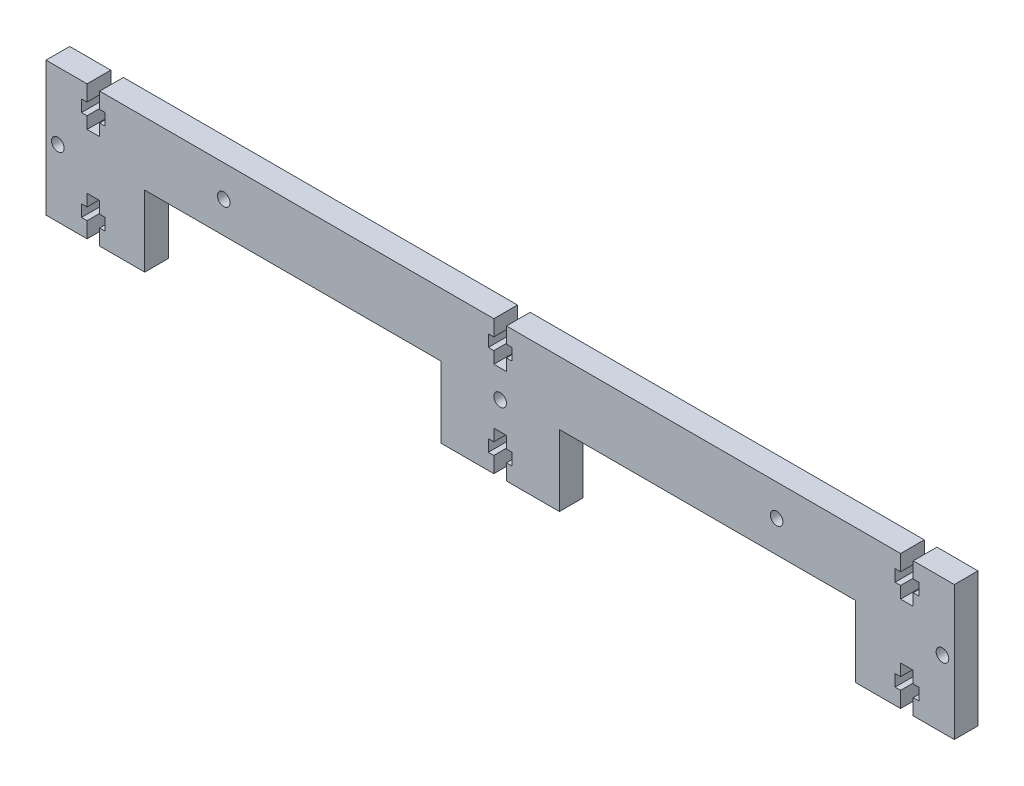
SolidWorks part; units mm, degrees
material "Balsa"
ref_plane "Plano frontal" through (0, 0, 0) normal (0, 0, 1) x (1, 0, 0)
ref_plane "Plano superior" through (0, 0, 0) normal (0, 1, 0) x (1, 0, 0)
ref_plane "Plano direito" through (0, 0, 0) normal (1, 0, 0) x (0, 0, -1)
sketch "Esboço1" plane through (0, 0, 0) normal (0, 0, 1) x (1, 0, 0)
  line L0 (-115, 0) -> (0, 0) construction
  line L1 (-115, 17) -> (-115, -17)
  line L2 (-115, -17) -> (-104.6, -17)
  line L3 (-104.6, -17) -> (-104.6, -13)
  line L4 (-104.6, -13) -> (-106, -13)
  line L5 (-106, -13) -> (-106, -10)
  line L6 (-106, -10) -> (-104.6, -10)
  line L7 (-104.6, -10) -> (-104.6, -7)
  line L8 (-104.6, -7) -> (-101.4, -7)
  line L9 (-101.4, -7) -> (-101.4, -10)
  line L10 (-101.4, -10) -> (-100, -10)
  line L11 (-100, -10) -> (-100, -13)
  line L12 (-100, -13) -> (-101.4, -13)
  line L13 (-101.4, -13) -> (-101.4, -17)
  line L14 (-101.4, -17) -> (-1.6, -17)
  line L15 (0, 0) -> (0, -33.0789) construction
  line L16 (-103, -7) -> (-103, -4.5212) construction
  line L17 (-103, 7) -> (-103, 4.5212) construction
  line L18 (-101.4, 17) -> (-1.6, 17)
  line L19 (-101.4, 13) -> (-101.4, 17)
  line L20 (-100, 13) -> (-101.4, 13)
  line L21 (-100, 10) -> (-100, 13)
  line L22 (-101.4, 10) -> (-100, 10)
  line L23 (-101.4, 7) -> (-101.4, 10)
  line L24 (-104.6, 7) -> (-101.4, 7)
  line L25 (-104.6, 10) -> (-104.6, 7)
  line L26 (-106, 10) -> (-104.6, 10)
  line L27 (-106, 13) -> (-106, 10)
  line L28 (-104.6, 13) -> (-106, 13)
  line L29 (-104.6, 17) -> (-104.6, 13)
  line L30 (-115, 17) -> (-104.6, 17)
  line L31 (103, 7) -> (103, 4.5212) construction
  line L32 (103, -7) -> (103, -4.5212) construction
  line L33 (115, 17) -> (104.6, 17)
  line L34 (104.6, 17) -> (104.6, 13)
  line L35 (104.6, 13) -> (106, 13)
  line L36 (106, 13) -> (106, 10)
  line L37 (106, 10) -> (104.6, 10)
  line L38 (104.6, 10) -> (104.6, 7)
  line L39 (104.6, 7) -> (101.4, 7)
  line L40 (101.4, 7) -> (101.4, 10)
  line L41 (101.4, 10) -> (100, 10)
  line L42 (100, 10) -> (100, 13)
  line L43 (100, 13) -> (101.4, 13)
  line L44 (101.4, 13) -> (101.4, 17)
  line L45 (101.4, -13) -> (101.4, -17)
  line L46 (100, -13) -> (101.4, -13)
  line L47 (100, -10) -> (100, -13)
  line L48 (101.4, -10) -> (100, -10)
  line L49 (101.4, -7) -> (101.4, -10)
  line L50 (104.6, -7) -> (101.4, -7)
  line L51 (104.6, -10) -> (104.6, -7)
  line L52 (106, -10) -> (104.6, -10)
  line L53 (106, -13) -> (106, -10)
  line L54 (104.6, -13) -> (106, -13)
  line L55 (104.6, -17) -> (104.6, -13)
  line L56 (115, -17) -> (104.6, -17)
  line L57 (115, 17) -> (115, -17)
  line L58 (-103, -4.5212) -> (0, -4.5212) construction
  line L59 (-51.5, -4.5212) -> (-51.5, -17) construction
  line L60 (0, 7) -> (0, 4.5212) construction
  line L61 (1.6, 17) -> (1.6, 13)
  line L62 (1.6, 13) -> (3, 13)
  line L63 (3, 13) -> (3, 10)
  line L64 (3, 10) -> (1.6, 10)
  line L65 (1.6, 10) -> (1.6, 7)
  line L66 (1.6, 7) -> (-1.6, 7)
  line L67 (-1.6, 7) -> (-1.6, 10)
  line L68 (-1.6, 10) -> (-3, 10)
  line L69 (-3, 10) -> (-3, 13)
  line L70 (-3, 13) -> (-1.6, 13)
  line L71 (-1.6, 13) -> (-1.6, 17)
  line L72 (-1.6, -13) -> (-1.6, -17)
  line L73 (-3, -13) -> (-1.6, -13)
  line L74 (-3, -10) -> (-3, -13)
  line L75 (-1.6, -10) -> (-3, -10)
  line L76 (-1.6, -7) -> (-1.6, -10)
  line L77 (1.6, -7) -> (-1.6, -7)
  line L78 (1.6, -10) -> (1.6, -7)
  line L79 (3, -10) -> (1.6, -10)
  line L80 (3, -13) -> (3, -10)
  line L81 (1.6, -13) -> (3, -13)
  line L82 (1.6, -17) -> (1.6, -13)
  line L83 (1.6, 17) -> (101.4, 17)
  line L84 (1.6, -17) -> (101.4, -17)
  circle A0 centre (112, 0) radius 1.6
  circle A1 centre (0, 0) radius 1.6
  circle A2 centre (-112, 0) radius 1.6
  point P56 (0, -30)
  dimension "D9" = 3.2
  dimension "D1" = 4
  dimension "D2" = 3.2
  dimension "D3" = 3
  dimension "D4" = 6
  dimension "D5" = 12
  dimension "D6" = 230
  dimension "D7" = 17
  dimension "D8" = 3
  dimension "D10" = 3
extrude "Ressalto-extrusão1" add sketch "Esboço1" along normal blind 6 contours L18 L71 L70 L69 L68 L67 L66 L65 L64 L63 L62 L61 L83 L44 L43 L42 L41 L40 L39 L38 L37 L36 L35 L34 L33 L57 L56 L55 L54 L53 L52 L51 L50 L49 L48 L47 L46 L45 L84 L82 L81 L80 L79 L78 L77 L76 L75 L74 L73 L72 L14 L13 L12 L11 L10 L9 L8 L7 L6 L5 L4 L3 L2 L1 L30 L29 L28 L27 L26 L25 L24 L23 L22 L21 L20 L19
sketch "Esboço2" plane through (0, 0, 6) normal (0, 0, 1) x (1, 0, 0)
  line L0 (1.6, -17) -> (101.4, -17) construction
  line L1 (90, -17) -> (15, -17)
  line L2 (90, -17) -> (90, 1)
  line L3 (90, 1) -> (15, 1)
  line L4 (15, -17) -> (15, 1)
  line L5 (0, 0) -> (0, 64.449) construction
  line L6 (-15, -17) -> (-15, 1)
  line L7 (-90, 1) -> (-15, 1)
  line L8 (-90, -17) -> (-90, 1)
  line L9 (-90, -17) -> (-15, -17)
  line L10 (115, -17) -> (115, 17) construction
  line L11 (101.4, 17) -> (1.6, 17) construction
  circle A0 centre (70, 9) radius 1.6
  circle A1 centre (-70, 9) radius 1.6
  dimension "D5" = 3.2
  dimension "D1" = 25
  dimension "D2" = 30
  dimension "D3" = 16
  dimension "D4" = 8
  dimension "D6" = 70
extrude "Corte-extrusão1" cut sketch "Esboço2" against normal blind 10
